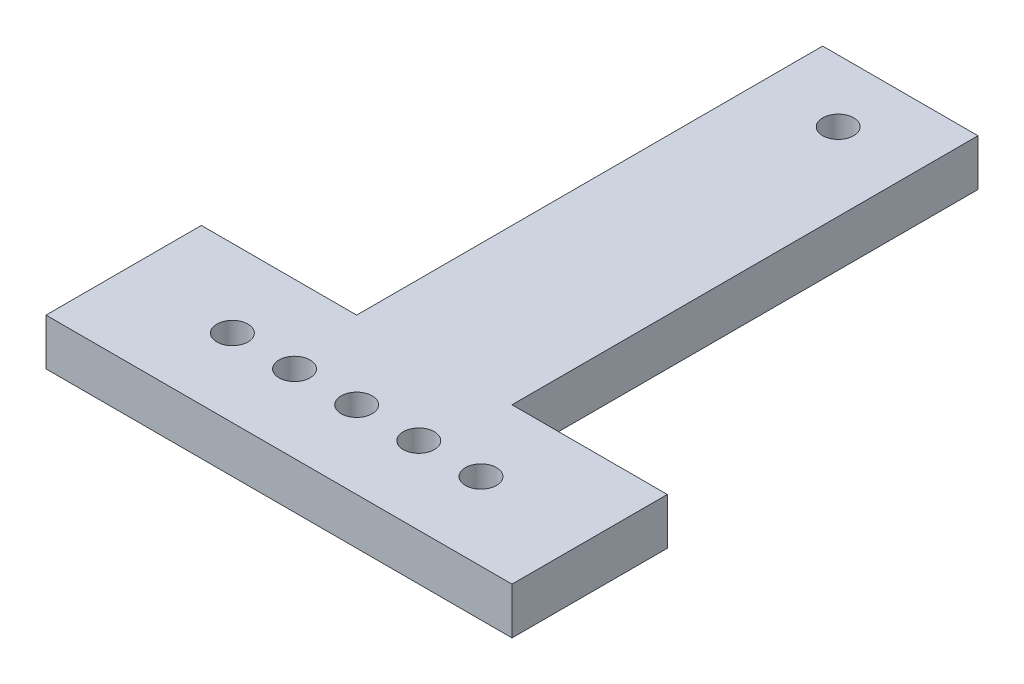
SolidWorks part; units mm, degrees
ref_plane "Front Plane" through (0, 0, 0) normal (0, 0, 1) x (1, 0, 0)
ref_plane "Top Plane" through (0, 0, 0) normal (0, 1, 0) x (1, 0, 0)
ref_plane "Right Plane" through (0, 0, 0) normal (1, 0, 0) x (0, 0, -1)
sketch "Sketch1" plane through (0, 0, 0) normal (0, 1, 0) x (1, 0, 0)
  line L1 (0, 0) -> (50, 0)
  line L2 (0, 0) -> (0, 200)
  line L3 (0, 200) -> (50, 200)
  line L4 (50, 0) -> (50, 200)
  dimension "D1" = 50
  dimension "D2" = 200
extrude "Boss-Extrude1" add sketch "Sketch1" along normal blind 15 contours L4 L3 L2 L1
sketch "Sketch2" plane through (0, 15, 0) normal (0, 1, 0) x (1, 0, 0)
  line L0 (0, 0) -> (50, 0) construction
  line L1 (0, 0) -> (0, 200) construction
  circle A0 centre (25, 180) radius 5
  dimension "D1" = 180
  dimension "D2" = 25
extrude "Cut-Extrude2" cut sketch "Sketch2" against normal through all
sketch "Sketch3" plane through (50, 0, 0) normal (1, 0, 0) x (0, 0, -1)
  line L0 (0, 15) -> (50, 15)
  line L1 (0, 15) -> (200, 15) construction
  line L2 (50, 15) -> (50, 0)
  line L3 (0, 0) -> (200, 0) construction
  line L4 (50, 0) -> (0, 0)
  line L6 (0, 0) -> (0, 15)
  dimension "D1" = 50
extrude "Boss-Extrude2" add sketch "Sketch3" along normal blind 50
sketch "Sketch4" plane through (0, 0, 0) normal (-1, 0, 0) x (0, 0, 1)
  line L0 (0, 0) -> (-200, 0) construction
  line L1 (0, 15) -> (-50, 15)
  line L2 (0, 15) -> (0, 0)
  line L3 (0, 0) -> (-50, 0)
  line L4 (-50, 15) -> (-50, 0)
  dimension "D1" = 50
extrude "Boss-Extrude3" add sketch "Sketch4" along normal blind 50
sketch "Sketch5" plane through (0, 15, 0) normal (0, 1, 0) x (1, 0, 0)
  line L0 (0, 0) -> (50, 0) construction
  line L1 (50, 0) -> (50, 200) construction
  circle A0 centre (25, 25) radius 5
  circle A1 centre (5, 25) radius 5
  circle A2 centre (-15, 25) radius 5
  circle A3 centre (45, 25) radius 5
  circle A4 centre (65, 25) radius 5
  dimension "D1" = 25
  dimension "D2" = 25
  dimension "D3" = 3
  dimension "D4" = 3
extrude "Cut-Extrude3" cut sketch "Sketch5" against normal through all contours A0 | A1 | A3 | A4 | A2
